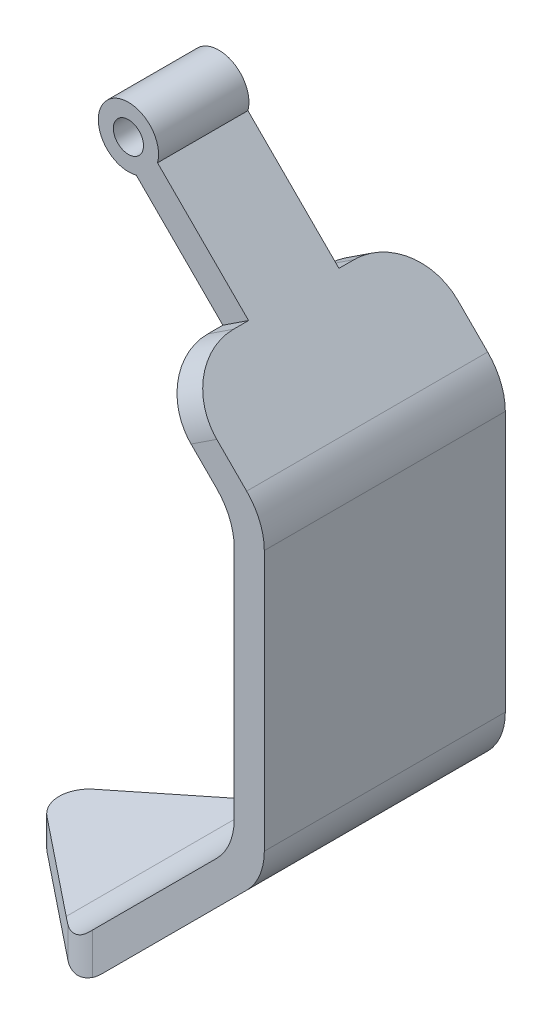
SolidWorks part; units mm, degrees
ref_plane "Front Plane" through (0, 0, 0) normal (0, 0, 1) x (1, 0, 0)
ref_plane "Top Plane" through (0, 0, 0) normal (0, 1, 0) x (1, 0, 0)
ref_plane "Right Plane" through (0, 0, 0) normal (1, 0, 0) x (0, 0, -1)
sketch "Sketch1" plane through (0, 0, 0) normal (0, 0, 1) x (1, 0, 0)
  line L0 (-25, 50) -> (25, 50)
  line L1 (25, -55) -> (52.052, -27.948)
  line L2 (-25, -55) -> (25, -55)
  line L3 (52.052, 19.4124) -> (52.052, -27.948)
  line L4 (-25, 60) -> (25, 60)
  line L5 (-25, 60) -> (-25, 50)
  line L6 (25, 60) -> (25, 50)
  line L7 (-101.1483, 0) -> (194.0125, 0) construction
  line L8 (23.7678, 54.7678) -> (57.052, 21.4835)
  line L9 (20.2322, 51.2322) -> (52.052, 19.4124)
  line L10 (57.052, 21.4835) -> (57.052, -30.019)
  line L11 (27.0711, -60) -> (57.052, -30.019)
  line L12 (-25, -60) -> (27.0711, -60)
  line L13 (0, -55) -> (0, -60)
  circle A1 centre (22, 53) radius 1.5
  circle A2 centre (22, 53) radius 2.5
  circle A3 centre (0, -5) radius 50
  circle A4 centre (22, 53) radius 5
  point P0 (0, -55)
  point P1 (0, 50)
  dimension "D1" = 10
  dimension "D2" = 3
  dimension "D4" = 5
  dimension "D5" = 50
  dimension "D7" = 3
  dimension "D13" = 100
  dimension "D16" = 10
  dimension "D3" = 3
  dimension "D6" = 50
  dimension "D8" = 55
  dimension "D9" = 45
  dimension "D10" = 45
  dimension "D11" = 5
  dimension "D12" = 45
  dimension "D14" = 50
  dimension "D15" = 5
extrude "Boss-Extrude1" add sketch "Sketch1" along normal blind 20 contours L6 A4 L0 L9 A2 L8 | L8 A4 L6 | L9 A4 L8 L6 L0 | A2 L9 L0 L6 L8 | L0 A4 L9 | L3 L7 L10 L8 A4 L9 | L7 L3 L1 L2 L13 L12 L11 L10
sketch "Sketch2" plane through (0, 0, 20) normal (0, 0, 1) x (1, 0, 0)
  line L0 (26.8296, 51.7059) -> (57.052, 21.4835)
  line L1 (23.2941, 48.1704) -> (52.052, 19.4124)
  line L2 (37.6731, 33.7914) -> (41.9408, 36.5947)
  circle A0 centre (22, 53) radius 5
  arc M2 (26.8296, 51.7059) -> (23.2941, 48.1704) centre (22, 53) ccw
  line M3 (23.2941, 48.1704) -> (52.052, 19.4124)
  circle M12 centre (22, 53) radius 2.5
extrude "Cut-Extrude1" cut sketch "Sketch2" against normal blind 12.5 contours A0 M2 M12 | A0 L2 L0 M3
sketch "Sketch3" plane through (0, -55, 0) normal (0, 1, 0) x (1, 0, 0)
  line L0 (25, -20) -> (0, 0)
  line L1 (25, -20) -> (0, -20)
  line L2 (0, -20) -> (0, 0)
extrude "Cut-Extrude2" cut sketch "Sketch3" against normal up to surface (5 mm away) up to face at (13.5355, -60, 10)
mirror "Mirror2" about plane through (0, 0, 0) normal (0, 0, 1) of "Boss-Extrude1", "Cut-Extrude2", "Cut-Extrude1"
fillet "Fillet5" radius 10 2 edges at (39.807, 35.193, -20) (39.807, 35.193, 20)
fillet "Fillet6" radius 10 3 edges at (27.0711, -60, 0) (57.052, -30.019, 0) (57.052, 21.4835, 0)
fillet "Fillet7" radius 10 3 edges at (25, -55, 0) (52.052, -27.948, 0) (52.052, 19.4124, 0)
fillet "Fillet8" radius 10 2 edges at (25, -56.9425, -20) (25, -56.9425, 20)
fillet "Fillet9" radius 5 1 edges at (0, -57.5, 0)
sketch "Sketch4" plane through (0, 0, 0) normal (0, 0, 1) x (1, 0, 0)
  line L0 (0, 71.5048) -> (0, -71.4406)
  line L1 (22.2609, -60) -> (-21.2167, -60)
  line L2 (22, 53) -> (-19.1525, 53)
